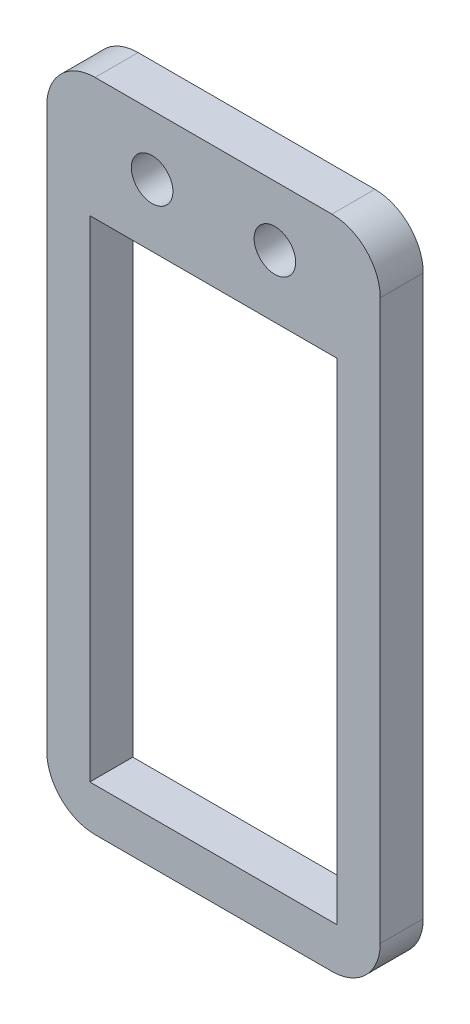
SolidWorks part; units mm, degrees
ref_plane "Front Plane" through (0, 0, 0) normal (0, 0, 1) x (1, 0, 0)
ref_plane "Top Plane" through (0, 0, 0) normal (0, 1, 0) x (1, 0, 0)
ref_plane "Right Plane" through (0, 0, 0) normal (1, 0, 0) x (0, 0, -1)
sketch "Sketch3" plane through (0, 0, -25.2783) normal (0, 0, 1) x (1, 0, 0)
  line L0 (19.05, -6.453) -> (6.35, -6.453) construction
  line L1 (29.95, -61.653) -> (-4.55, -61.653)
  line L2 (29.95, -61.653) -> (29.95, 6.2)
  line L3 (29.95, 6.2) -> (-4.55, 6.2)
  line L4 (-4.55, -61.653) -> (-4.55, 6.2)
  line L5 (25.5, -57.203) -> (-0.1, -57.203)
  line L6 (25.5, -57.203) -> (25.5, -6.453)
  line L7 (25.5, -6.453) -> (-0.1, -6.453)
  line L8 (-0.1, -57.203) -> (-0.1, -6.453)
  line L9 (19.05, -56.803) -> (6.35, -56.803) construction
  line L11 (16.0717, 6.2) -> (25.4, 6.2) construction
  line L12 (6.35, 0) -> (29.95, 0) construction
  line L16 (25.3, -6.453) -> (25.3, -57.203) construction
  line L17 (0.1, -6.453) -> (0.1, -57.203) construction
  circle A0 centre (6.35, 0) radius 2.15
  arc A1 (8.0467, -2.6837) -> (3.4527, -1.2985) centre (6.35, 0) ccw construction
  arc A2 (3.175, 0) -> (9.525, 0) centre (6.35, 0) ccw construction
  circle A3 centre (19.05, 0) radius 2.15
  arc A4 (16.1657, 1.3272) -> (16.3558, -1.6798) centre (19.05, 0) cw construction
  arc A5 (22.225, 0) -> (15.875, 0) centre (19.05, 0) ccw construction
  arc A6 (15.875, 0) -> (22.225, 0) centre (19.05, 0) ccw construction
  dimension "D5" = 4.3
  dimension "D1" = 0.4
  dimension "D2" = 4.45
  dimension "D3" = 4.45
  dimension "D4" = 4.45
  dimension "D6" = 0.2
  dimension "D7" = 0.2
extrude "Boss-Extrude1" add sketch "Sketch3" along normal blind 4.45
fillet "Fillet1" radius 5 4 edges at (-4.55, -61.653, -23.0533) (29.95, -61.653, -23.0533) (29.95, 6.2, -23.0533) (-4.55, 6.2, -23.0533)
